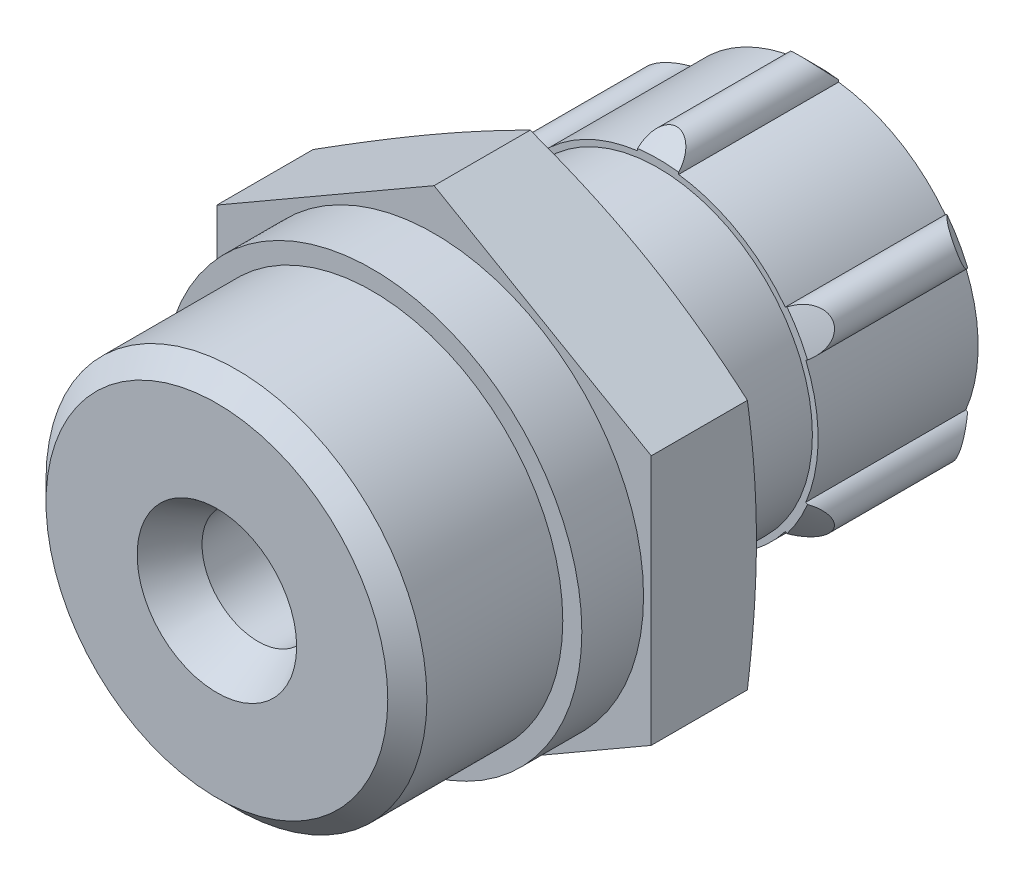
SolidWorks part; units mm, degrees
ref_plane "Front Plane" through (0, 0, 0) normal (0, 0, 1) x (1, 0, 0)
ref_plane "Top Plane" through (0, 0, 0) normal (0, 1, 0) x (1, 0, 0)
ref_plane "Right Plane" through (0, 0, 0) normal (1, 0, 0) x (0, 0, -1)
ref_plane "Plane1" through (0, 0, 0) normal (1, 0, 0) x (0, 0, -1)
sketch "Sketch1" plane through (0, 0, 0) normal (1, 0, 0) x (0, 0, -1)
  line L0 (15.3, 0) -> (15.3, 6.75)
  line L1 (15.3, 6.75) -> (26.3, 6.75)
  line L2 (26.3, 6.75) -> (26.3, 0)
  line L3 (26.3, 0) -> (15.3, 0)
  line L4 (26.3, 0) -> (15.3, 0) construction
revolve "Revolve1" add sketch "Sketch1" angle 360 about L4
ref_plane "Plane2" through (0, 0, 0) normal (1, 0, 0) x (0, 0, -1)
sketch "Sketch2" plane through (0, 0, 0) normal (1, 0, 0) x (0, 0, -1)
  line L0 (15.3, 0) -> (15.3, 6)
  line L1 (15.3, 6) -> (15.8415, 5.4585)
  line L2 (15.8415, 5.4585) -> (24.3, 5.4585)
  line L3 (24.3, 5.4585) -> (25.6085, 4.15)
  line L4 (25.6085, 4.15) -> (26.3, 4.15)
  line L5 (26.3, 4.15) -> (26.3, 0)
  line L6 (26.3, 0) -> (15.3, 0)
  line L7 (26.3, 0) -> (15.3, 0) construction
revolve "Cut-Revolve1" cut sketch "Sketch2" angle 360 about L7
cosmetic thread "Cosmetic Thread1" parameters "D1"=1.1585, "D2"=12
ref_plane "Plane3" through (0, 0, -19.3) normal (0, 0, 1) x (1, 0, 0)
sketch "Sketch3" plane through (0, 0, -19.3) normal (0, 0, 1) x (1, 0, 0)
  arc A0 (-6.4611, 2.6933) -> (-6.4611, -2.6933) centre (0, 0) ccw
  arc A1 (-6.4611, -2.6933) -> (-5.563, -4.2489) centre (-6.0622, -3.5) ccw
  arc A2 (-5.563, -4.2489) -> (-0.8981, -6.9421) centre (0, 0) ccw
  arc A3 (-0.8981, -6.9421) -> (0.8981, -6.9421) centre (0, -7) ccw
  arc A4 (0.8981, -6.9421) -> (5.563, -4.2489) centre (0, 0) ccw
  arc A5 (5.563, -4.2489) -> (6.4611, -2.6933) centre (6.0622, -3.5) ccw
  arc A6 (6.4611, -2.6933) -> (6.4611, 2.6933) centre (0, 0) ccw
  arc A7 (6.4611, 2.6933) -> (5.563, 4.2489) centre (6.0622, 3.5) ccw
  arc A8 (5.563, 4.2489) -> (0.8981, 6.9421) centre (0, 0) ccw
  arc A9 (0.8981, 6.9421) -> (-0.8981, 6.9421) centre (0, 7) ccw
  arc A10 (-0.8981, 6.9421) -> (-5.563, 4.2489) centre (0, 0) ccw
  arc A11 (-5.563, 4.2489) -> (-6.4611, 2.6933) centre (-6.0622, 3.5) ccw
  circle A12 centre (0, 0) radius 6.075
extrude "Boss-Extrude1" add sketch "Sketch3" against normal blind 7
ref_plane "Plane4" through (0, 0, 0) normal (1, 0, 0) x (0, 0, -1)
sketch "Sketch4" plane through (0, 0, 0) normal (1, 0, 0) x (0, 0, -1)
  line L0 (18.3, 20.5875) -> (18.3, 7.0875)
  line L1 (18.3, 7.0875) -> (19.3, 7.0875)
  line L2 (19.3, 7.0875) -> (22.8, 10.5875)
  line L3 (22.8, 10.5875) -> (27.3, 6.0875)
  line L4 (27.3, 6.0875) -> (27.3, 20.5875)
  line L5 (27.3, 20.5875) -> (18.3, 20.5875)
  line L6 (27.3, 0) -> (18.3, 0) construction
revolve "Cut-Revolve2" cut sketch "Sketch4" angle 360 about L6
ref_plane "Plane5" through (0, 0, 0) normal (1, 0, 0) x (0, 0, -1)
sketch "Sketch5" plane through (0, 0, 0) normal (1, 0, 0) x (0, 0, -1)
  line L0 (0, 0) -> (0, 7.475)
  line L1 (0, 7.475) -> (0.856, 8.331)
  line L2 (0.856, 8.331) -> (6.8, 8.331)
  line L3 (6.8, 8.331) -> (6.8, 9.1641)
  line L4 (6.8, 9.1641) -> (9.5, 9.1641)
  line L5 (9.5, 9.1641) -> (9.5, 11.4)
  line L6 (9.5, 11.4) -> (13.5909, 11.4)
  line L7 (13.5909, 11.4) -> (14.1, 9.5)
  line L8 (14.1, 9.5) -> (14.1, 6.4)
  line L9 (14.5, 6) -> (20.1, 6)
  line L10 (20.1, 6) -> (21.1, 5)
  line L11 (21.1, 5) -> (21.1, 3.6)
  line L12 (21.3, 3.4) -> (25, 3.4)
  line L13 (25.2826, 3.6479) -> (27.2, 2.95)
  line L14 (27.2, 2.95) -> (28, 2.95)
  line L15 (28.3, 2.65) -> (28.3, 0)
  line L16 (28.3, 0) -> (0, 0)
  line L17 (28.3, 0) -> (0, 0) construction
  arc A0 (14.1, 6.4) -> (14.5, 6) centre (14.5, 6.4) ccw
  arc A1 (21.1, 3.6) -> (21.3, 3.4) centre (21.3, 3.6) ccw
  arc A2 (25, 3.4) -> (25.2826, 3.6479) centre (25.25, 3.4) cw
  arc A3 (28, 2.95) -> (28.3, 2.65) centre (28, 2.65) cw
revolve "Revolve2" add sketch "Sketch5" angle 360 about L17
cosmetic thread "Cosmetic Thread2" parameters "D1"=6.8, "D2"=14.95
ref_plane "Plane6" through (0, 0, -14.1) normal (0, 0, 1) x (1, 0, 0)
sketch "Sketch6" plane through (0, 0, -14.1) normal (0, 0, 1) x (1, 0, 0)
  line L0 (-19, -19) -> (19, -19)
  line L1 (19, -19) -> (19, 19)
  line L2 (19, 19) -> (-19, 19)
  line L3 (-19, 19) -> (-19, -19)
  line L4 (-9.5, 5.4848) -> (-9.5, -5.4848)
  line L5 (-9.5, -5.4848) -> (0, -10.9697)
  line L6 (0, -10.9697) -> (9.5, -5.4848)
  line L7 (9.5, -5.4848) -> (9.5, 5.4848)
  line L8 (9.5, 5.4848) -> (0, 10.9697)
  line L9 (0, 10.9697) -> (-9.5, 5.4848)
extrude "Cut-Extrude1" cut sketch "Sketch6" along normal blind 4.6
ref_plane "Plane7" through (0, 0, 0) normal (1, 0, 0) x (0, 0, -1)
sketch "Sketch7" plane through (0, 0, 0) normal (1, 0, 0) x (0, 0, -1)
  line L0 (0, 0) -> (0, 3.4892)
  line L1 (0, 3.4892) -> (1.8, 2.45)
  line L2 (1.8, 2.45) -> (28.3, 2.45)
  line L3 (28.3, 2.45) -> (28.3, 0)
  line L4 (28.3, 0) -> (0, 0)
  line L5 (28.3, 0) -> (0, 0) construction
revolve "Cut-Revolve3" cut sketch "Sketch7" angle 360 about L5
